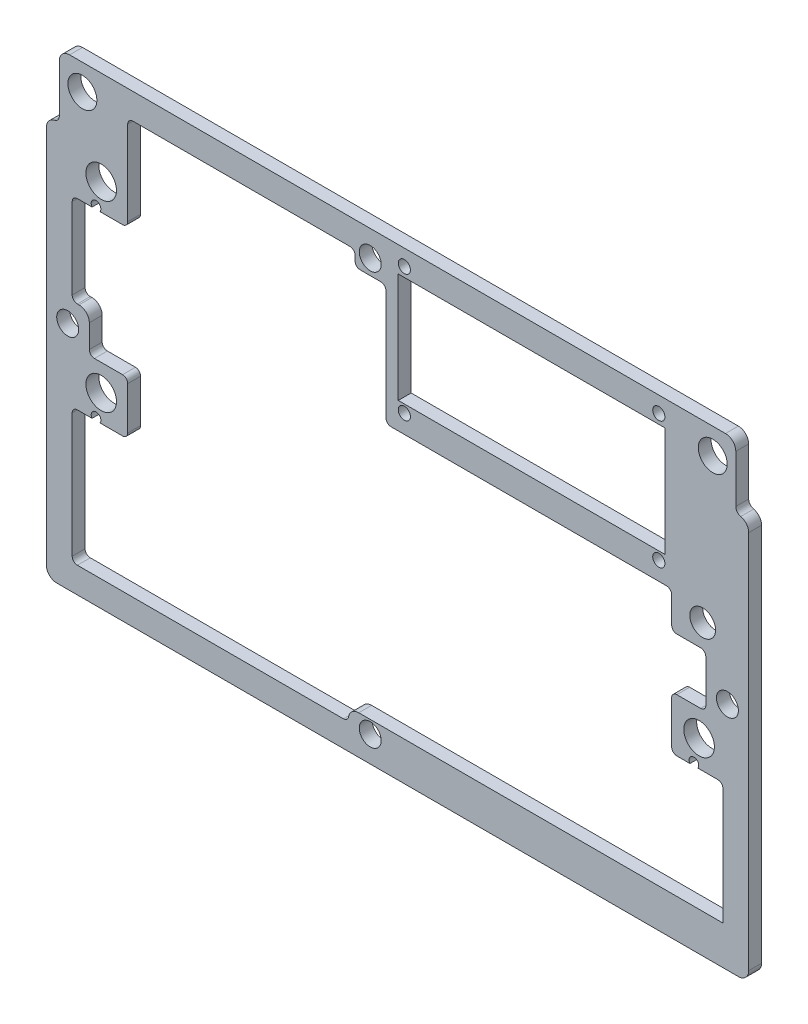
SolidWorks part; units mm, degrees
material "ABS PC"
ref_plane "Front Plane" through (0, 0, 0) normal (0, 0, 1) x (1, 0, 0)
ref_plane "Top Plane" through (0, 0, 0) normal (0, 1, 0) x (1, 0, 0)
ref_plane "Right Plane" through (0, 0, 0) normal (1, 0, 0) x (0, 0, -1)
sketch "Sketch1" plane through (0, 0, 0) normal (0, 0, 1) x (1, 0, 0)
  line L0 (94.968, 16.637) -> (-44.732, 16.637) construction
  line L1 (-61.4007, -97.663) -> (111.6368, -97.663)
  line L2 (-61.4007, -97.663) -> (-61.4007, 16.637)
  line L3 (-61.4007, 16.637) -> (111.6368, 16.637)
  line L4 (111.6368, -97.663) -> (111.6368, 16.637)
  line L5 (-61.4007, -97.663) -> (111.6368, 16.637) construction
  line L6 (-61.4007, 16.637) -> (111.6368, -97.663) construction
  point P4 (25.118, -40.513)
extrude "Boss-Extrude1" add sketch "Sketch1" along normal blind 3.175
sketch "Sketch3" plane through (0, 0, 3.175) normal (0, 0, 1) x (1, 0, 0)
  circle A0 centre (100.302, -26.543) radius 3.175
  circle A1 centre (99.413, -51.6255) radius 3.7703
  circle A2 centre (-47.907, -51.6255) radius 3.7703
  circle A3 centre (-47.907, -6.5405) radius 3.7703
  dimension "D1" = 6.35
  dimension "D2" = 7.5406
extrude "Cut-Extrude1" cut sketch "Sketch3" against normal through all
hole_wizard "#6 Clearance Hole1" positions "Sketch5" profile "Sketch4" hole size "#6" standard "ANSI Inch" end condition through all
sketch "Sketch5" plane through (0, 0, 3.175) normal (0, 0, 1) x (1, 0, 0)
  point P0 (18.387, 10.287)
  point P3 (-56.162, -40.894)
  point P6 (106.398, -40.894)
  point P9 (18.387, -91.313)
sketch "Sketch4" plane through (18.387, 10.287, 3.175) normal (1, 0, 0) x (0, -1, 0)
  line L0 (0, 0) -> (0, 3.175)
  line L1 (0, 3.175) -> (2.1526, 3.175)
  line L2 (2.1526, 3.175) -> (2.1526, 0)
  line L5 (2.1526, 0) -> (0, 0)
  line L11 (0, -6.35) -> (0, 107.95) construction
  dimension "Thru Hole Dia." = 4.3053
  dimension "Thru Hole Depth" = 3.175
hole_wizard "#2 Clearance Hole1" positions "Sketch7" profile "Sketch6" hole size "#2" standard "ANSI Inch" end condition through all
sketch "Sketch7" plane through (0, 0, 3.175) normal (0, 0, 1) x (1, 0, 0)
  point P0 (26.788, 12.7)
  point P3 (89.488, 12.7)
  point P6 (89.488, -18.6)
  point P9 (26.788, -18.6)
sketch "Sketch6" plane through (26.788, 12.7, 3.175) normal (1, 0, 0) x (0, -1, 0)
  line L0 (0, 0) -> (0, 3.175)
  line L1 (0, 3.175) -> (1.3525, 3.175)
  line L2 (1.3525, 3.175) -> (1.3525, 0)
  line L5 (1.3525, 0) -> (0, 0)
  line L11 (0, -6.35) -> (0, 107.95) construction
  dimension "Thru Hole Dia." = 2.7051
  dimension "Thru Hole Depth" = 3.175
sketch "Sketch8" plane through (0, 0, 3.175) normal (0, 0, 1) x (1, 0, 0)
  line L9 (92.658, -23.1276) -> (22.2605, -23.1276)
  line L10 (22.2605, -23.1276) -> (22.2605, 6.5468)
  line L11 (22.2605, 6.5468) -> (14.6469, 6.5468)
  line L12 (92.658, -23.1276) -> (92.658, -32.1509)
  line L13 (28.768, 10.37) -> (28.768, -16.62)
  line L14 (28.768, -16.62) -> (87.508, -16.62)
  line L15 (87.508, -16.62) -> (87.508, 10.37)
  line L16 (87.508, 10.37) -> (28.768, 10.37)
  line L17 (28.768, 10.37) -> (28.768, -16.62)
  line L18 (28.768, -16.62) -> (87.508, -16.62)
  line L19 (87.508, -16.62) -> (87.508, 10.37)
  line L20 (87.508, 10.37) -> (28.768, 10.37)
  line L21 (92.658, -32.1509) -> (101.0704, -32.1509)
  line L22 (101.0704, -32.1509) -> (101.0704, -45.0855)
  line L23 (101.0704, -45.0855) -> (92.658, -45.0855)
  line L24 (92.658, -45.0855) -> (92.658, -58.1655)
  line L25 (92.658, -58.1655) -> (105.2868, -58.1655)
  line L26 (105.2868, -58.1655) -> (105.2868, -88.138)
  line L27 (105.2868, -88.138) -> (13.0594, -88.138)
  line L28 (13.0594, -88.138) -> (13.0594, -91.313)
  line L29 (13.0594, -91.313) -> (-55.0507, -91.313)
  line L30 (-55.0507, -91.313) -> (-55.0507, -58.1655)
  line L31 (-55.0507, -58.1655) -> (-41.367, -58.1655)
  line L32 (-41.367, -58.1655) -> (-41.367, -45.0855)
  line L33 (-41.367, -45.0855) -> (-50.8343, -45.0855)
  line L34 (-50.8343, -45.0855) -> (-50.8343, -35.5664)
  line L35 (-50.8343, -35.5664) -> (-55.0507, -35.5664)
  line L36 (-55.0507, -35.5664) -> (-55.0507, -13.0805)
  line L37 (-55.0507, -13.0805) -> (-41.367, -13.0805)
  line L38 (-41.367, -13.0805) -> (-41.367, 10.287)
  line L39 (14.6469, 6.5468) -> (14.6469, 10.287)
  line L40 (14.6469, 10.287) -> (-41.367, 10.287)
  line L43 (92.658, -45.0855) -> (109.0968, -45.0855) construction
  line L44 (111.6368, -97.663) -> (111.6368, 16.637) construction
  line L45 (-61.4007, -97.663) -> (111.6368, -97.663) construction
  line L46 (-61.4007, 16.637) -> (-61.4007, -97.663) construction
  line L47 (111.6368, 16.637) -> (-61.4007, 16.637) construction
  circle A1 centre (106.398, -40.894) radius 2.1526 construction
  circle A3 centre (18.387, -91.313) radius 2.1526 construction
  circle A8 centre (-56.162, -40.894) radius 2.1526 construction
  circle A11 centre (18.387, 10.287) radius 2.1526 construction
  circle A13 centre (26.788, -18.6) radius 1.3525 construction
  dimension "D1" = 1.27
  dimension "D10" = 1.5875
  dimension "D2" = 3.175
  dimension "D3" = 6.35
  dimension "D4" = 9.525
  dimension "D5" = 3.175
  dimension "D6" = 6.35
  dimension "D7" = 6.35
  dimension "D8" = 3.175
  dimension "D9" = 3.175
  dimension "D11" = 1.5875
  dimension "D12" = 6.35
  dimension "D13" = 3.175
  dimension "D14" = 3.175
extrude "Cut-Extrude2" cut sketch "Sketch8" against normal through all contours L19 L20 L17 L18 | L39 L40 L38 L37 L36 L35 L34 L33 L32 L31 L30 L29 L28 L27 L26 L25 L24 L23 L22 L21 L12 L9 L10 L11
hole_wizard "#3 (0.213) Diameter Hole1" positions "3DSketch1" profile "Sketch9" hole size "#3" standard "ANSI Inch" end condition through all
sketch3d "3DSketch1"
  line L0 (18.387, 10.287, 0) -> (18.387, 10.287, 3.175) construction
  line L1 (-56.162, -40.894, 0) -> (-56.162, -40.894, 3.175) construction
  line L2 (18.387, -91.313, 0) -> (18.387, -91.313, 3.175) construction
  line L3 (106.398, -40.894, 0) -> (106.398, -40.894, 3.175) construction
  point P0 (18.387, 10.287, 3.175)
  point P5 (-56.162, -40.894, 3.175)
  point P9 (18.387, -91.313, 3.175)
  point P13 (106.398, -40.894, 3.175)
sketch "Sketch9" plane through (18.387, 10.287, 3.175) normal (1, 0, 0) x (0, -1, 0)
  line L0 (0, 0) -> (0, 3.175)
  line L1 (0, 3.175) -> (2.7051, 3.175)
  line L2 (2.7051, 3.175) -> (2.7051, 0)
  line L5 (2.7051, 0) -> (0, 0)
  line L11 (0, -6.35) -> (0, 107.95) construction
  dimension "Thru Hole Dia." = 5.4102
  dimension "Thru Hole Depth" = 3.175
hole_wizard "Ø3.0 (3) Diameter Hole1" positions "Sketch11" profile "Sketch10" hole size "Ø3.0" standard "ANSI Metric" end condition through all
sketch "Sketch11" plane through (0, 0, 3.175) normal (0, 0, 1) x (1, 0, 0)
  point P0 (26.788, 12.7)
  point P3 (89.488, 12.7)
  point P6 (89.488, -18.6)
  point P9 (26.788, -18.6)
sketch "Sketch10" plane through (26.788, 12.7, 3.175) normal (1, 0, 0) x (0, -1, 0)
  line L0 (0, 0) -> (0, 3.175)
  line L1 (0, 3.175) -> (1.5, 3.175)
  line L2 (1.5, 3.175) -> (1.5, 0)
  line L5 (1.5, 0) -> (0, 0)
  line L11 (0, -6.35) -> (0, 107.95) construction
  dimension "Thru Hole Dia." = 3
  dimension "Thru Hole Depth" = 3.175
fillet "Fillet1" radius 1.27 21 edges at (-41.367, 10.287, 1.5875) (-41.367, -13.0805, 1.5875) (-55.0507, -13.0805, 1.5875) (-55.0507, -35.5664, 1.5875) (-50.8343, -45.0855, 1.5875) (-41.367, -45.0855, 1.5875) (-41.367, -58.1655, 1.5875) (-55.0507, -58.1655, 1.5875) (-55.0507, -91.313, 1.5875) (13.0594, -91.313, 1.5875) (105.2868, -58.1655, 1.5875) (92.658, -58.1655, 1.5875) (92.658, -45.0855, 1.5875) (101.0704, -45.0855, 1.5875) (101.0704, -32.1509, 1.5875) (92.658, -32.1509, 1.5875) (92.658, -23.1276, 1.5875) (22.2605, -23.1276, 1.5875) (14.6469, 6.5468, 1.5875) (22.2605, 6.5468, 1.5875) (14.6469, 10.287, 1.5875)
fillet "Fillet2" radius 2.54 6 edges at (13.0594, -88.138, 1.5875) (-50.8343, -35.5664, 1.5875) (111.6368, 16.637, 1.5875) (111.6368, -97.663, 1.5875) (-61.4007, -97.663, 1.5875) (-61.4007, 16.637, 1.5875)
hole_wizard "1/4 Clearance Hole1" positions "Sketch12" profile "Sketch13" hole size "1/4" standard "ANSI Inch" end condition up to next
sketch "Sketch12" plane through (0, 0, 0) normal (0, 0, -1) x (-1, 0, 0)
  point P0 (-102.7785, 10.287)
  point P2 (52.5425, 10.287)
sketch "Sketch13" plane through (102.7785, 10.287, 0) normal (1, 0, 0) x (0, 1, 0)
  line L0 (0, 0) -> (0, 3.175)
  line L1 (0, 3.175) -> (3.5712, 3.175)
  line L2 (3.5712, 3.175) -> (3.5712, 0)
  line L5 (3.5712, 0) -> (0, 0)
  line L11 (0, -6.35) -> (0, 107.95) construction
  dimension "Thru Hole Dia." = 7.1425
  dimension "Thru Hole Depth" = 3.175
sketch "Sketch14" plane through (0, 0, 0) normal (0, 0, -1) x (-1, 0, 0)
  line L0 (-111.6368, -95.123) -> (-111.6368, 14.097) construction
  line L1 (-111.6368, 0.762) -> (-108.4618, 0.762)
  line L2 (-111.6368, 0.762) -> (-111.6368, 16.637)
  line L3 (-111.6368, 16.637) -> (-108.4618, 16.637)
  line L4 (-108.4618, 0.762) -> (-108.4618, 16.637)
  line L5 (-109.0967, 16.637) -> (58.8607, 16.637) construction
  line L6 (-25.118, -97.663) -> (-25.118, 16.637) construction
  line L7 (58.8607, -97.663) -> (-109.0967, -97.663) construction
  line L8 (58.2257, 0.762) -> (58.2257, 16.637)
  line L9 (61.4008, 16.637) -> (58.2257, 16.637)
  line L10 (61.4008, 0.762) -> (61.4008, 16.637)
  line L11 (61.4008, 0.762) -> (58.2257, 0.762)
  dimension "D1" = 3.175
  dimension "D2" = 15.875
extrude "Cut-Extrude3" cut sketch "Sketch14" against normal up to next
fillet "Fillet3" radius 1.5875 2 edges at (-58.2257, 0.762, 1.5875) (108.4618, 0.762, 1.5875)
fillet "Fillet4" radius 2.54 4 edges at (111.6368, 0.762, 1.5875) (108.4617, 16.637, 1.5875) (-58.2257, 16.637, 1.5875) (-61.4008, 0.762, 1.5875)
sketch "Sketch15" plane through (0, 0, 0) normal (0, 0, -1) x (-1, 0, 0)
  line L0 (-28.768, -16.62) -> (-87.508, -16.62) construction
  line L1 (-90.988, 10.37) -> (-25.288, 10.37)
  line L2 (-90.988, 10.37) -> (-90.988, -16.62)
  line L3 (-90.988, -16.62) -> (-25.288, -16.62)
  line L4 (-25.288, 10.37) -> (-25.288, -16.62)
  line L5 (-87.508, 10.37) -> (-28.768, 10.37) construction
  line L6 (-90.988, 12.7) -> (-90.988, -18.6) construction
  line L7 (-25.288, 12.7) -> (-25.288, -18.6) construction
  circle A0 centre (-89.488, 12.7) radius 1.5 construction
  circle A1 centre (-89.488, -18.6) radius 1.5 construction
  circle A2 centre (-26.788, 12.7) radius 1.5 construction
  circle A3 centre (-26.788, -18.6) radius 1.5 construction
  dimension "D1" = 65.7
extrude "Cut-Extrude4" cut sketch "Sketch15" against normal up to next
sketch "Sketch16" plane through (0, 0, 0) normal (0, 0, -1) x (-1, 0, 0)
  circle A0 centre (-98.1425, -57.4894) radius 1.1906
  circle A1 centre (49.1775, -57.4894) radius 1.1906
  circle A2 centre (49.1775, -12.4044) radius 1.1906
  dimension "D1" = 2.3813
extrude "Cut-Extrude5" cut sketch "Sketch16" against normal up to next
